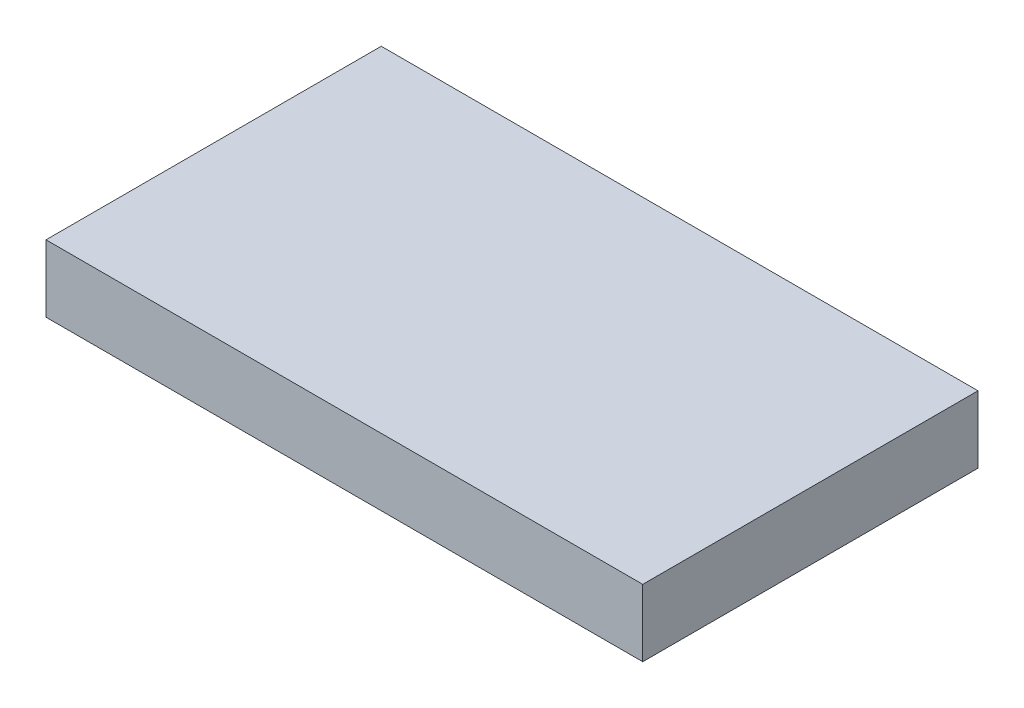
SolidWorks part; units mm, degrees
ref_plane "Front" through (0, 0, 0) normal (0, 0, 1) x (1, 0, 0)
ref_plane "Top" through (0, 0, 0) normal (0, 1, 0) x (1, 0, 0)
ref_plane "Right" through (0, 0, 0) normal (1, 0, 0) x (0, 0, -1)
sketch "草图1" plane through (0, 0, 0) normal (0, 1, 0) x (1, 0, 0)
  line L1 (0, 0) -> (180, 0)
  line L2 (0, 0) -> (0, 100)
  line L3 (0, 100) -> (180, 100)
  line L4 (180, 0) -> (180, 100)
  dimension "D1" = 100
  dimension "D2" = 180
extrude "凸台-拉伸2" add sketch "草图1" along normal blind 20 contours L3 L4 L1 L2
sketch "草图4" plane through (180, 0, 0) normal (1, 0, 0) x (0, 0, -1)
  line L0 (0, 20) -> (100, 20) construction
  line L3 (0, 20) -> (0, 0) construction
  arc A0 (20, 6.2) -> (20, 13.8) centre (20, 10) cw
  arc A1 (78, 6.2) -> (78, 13.8) centre (78, 10) ccw
  circle A2 centre (50, 10) radius 6
  dimension "D1" = 10
  dimension "D2" = 50
  dimension "D4" = 28
extrude "切除-拉伸3" cut sketch "草图4" against normal blind 2
sketch "草图5" plane through (178, 0, 0) normal (1, 0, 0) x (0, 0, -1)
  line L0 (18.597, 15) -> (50, 17.5)
  line L1 (100, 0) -> (100, 20)
  line L2 (50, 17.5) -> (77.691, 15)
  line L3 (77.691, 5) -> (50, 2.5)
  line L4 (50, 2.5) -> (18.597, 5)
  circle A0 centre (50, 10) radius 7.5
  arc A1 (18.597, 5) -> (18.597, 15) centre (18.597, 10) cw
  arc A2 (77.691, 5) -> (77.691, 15) centre (77.691, 10) ccw
